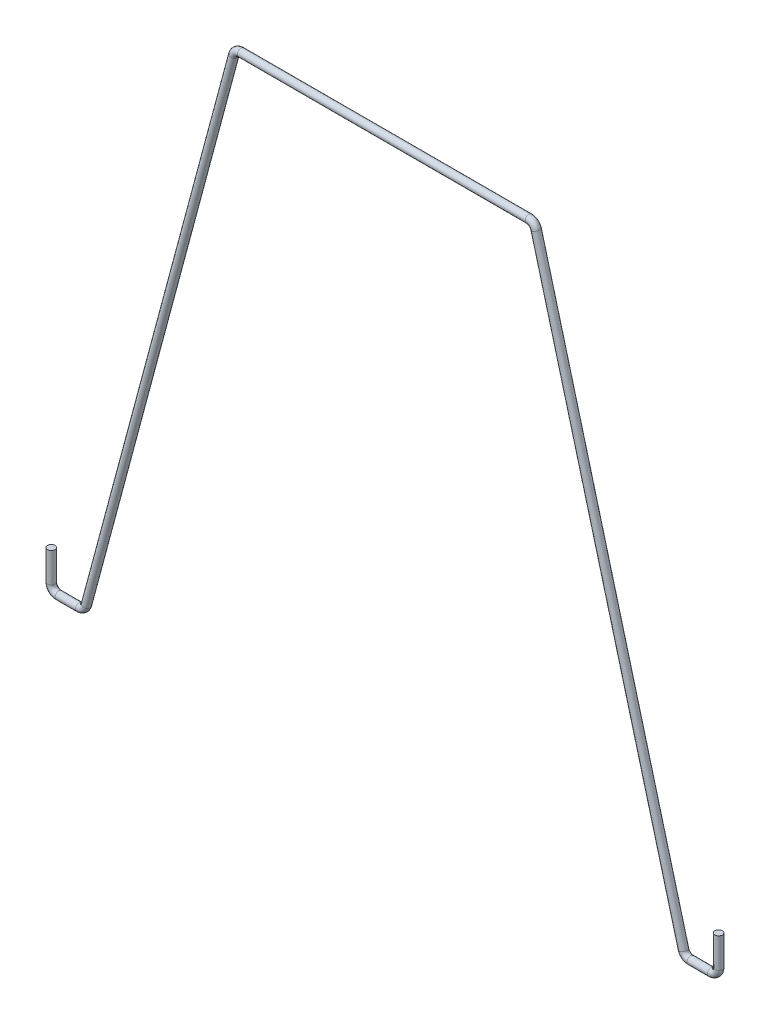
SolidWorks part; units mm, degrees
material "AISI 304"
ref_plane "Front Plane" through (0, 0, 0) normal (0, 0, 1) x (1, 0, 0)
ref_plane "Top Plane" through (0, 0, 0) normal (0, 1, 0) x (1, 0, 0)
ref_plane "Right Plane" through (0, 0, 0) normal (1, 0, 0) x (0, 0, -1)
sketch "Sketch1" plane through (0, 0, 0) normal (0, 0, 1) x (1, 0, 0)
  line L0 (9.7702, 0) -> (-9.7702, 0)
  line L1 (-10.2609, -0.3765) -> (-20.268, -37.7235)
  line L2 (-20.7587, -38.1) -> (-22.1469, -38.1)
  line L3 (-22.6549, -37.592) -> (-22.6549, -35.56)
  line L4 (0, 0) -> (0, -12.2334) construction
  line L5 (22.6549, -37.592) -> (22.6549, -35.56)
  line L6 (20.7587, -38.1) -> (22.1469, -38.1)
  line L7 (10.2609, -0.3765) -> (20.268, -37.7235)
  arc A0 (-22.1469, -38.1) -> (-22.6549, -37.592) centre (-22.1469, -37.592) cw
  arc A1 (-20.268, -37.7235) -> (-20.7587, -38.1) centre (-20.7587, -37.592) cw
  arc A2 (-9.7702, 0) -> (-10.2609, -0.3765) centre (-9.7702, -0.508) ccw
  arc A3 (9.7702, 0) -> (10.2609, -0.3765) centre (9.7702, -0.508) cw
  arc A4 (20.268, -37.7235) -> (20.7587, -38.1) centre (20.7587, -37.592) ccw
  arc A5 (22.1469, -38.1) -> (22.6549, -37.592) centre (22.1469, -37.592) ccw
  point P8 (-22.6549, -38.1)
  point P11 (-20.3689, -38.1)
  point P14 (-10.16, 0)
  dimension "D6" = 0.508
  dimension "D1" = 38.1
  dimension "D2" = 2.286
  dimension "D3" = 2.54
  dimension "D4" = 10.16
  dimension "D5" = 105
sweep "Sweep1" add path "Sketch1" circular profile diameter 0.508 parameters "D3"=0.508
